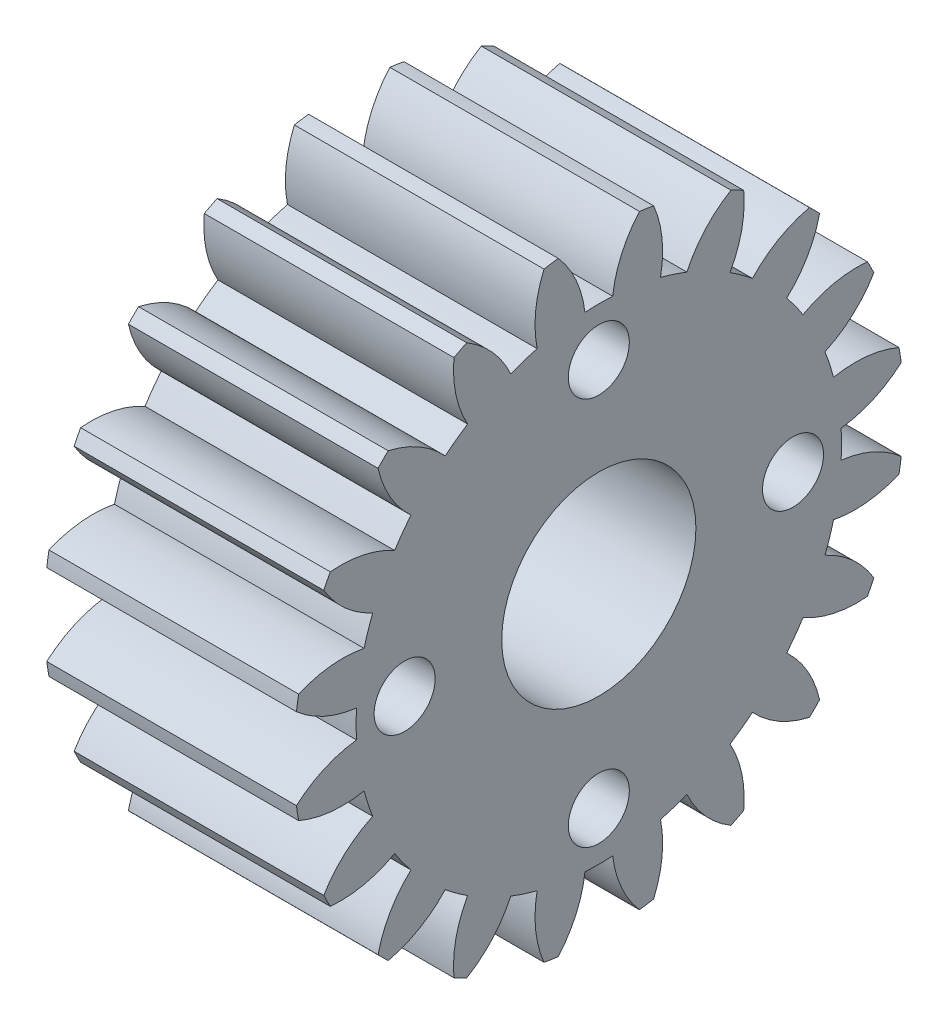
SolidWorks part; units mm, degrees
ref_plane "Plane1" through (0, 0, 0) normal (0, 0, 1) x (1, 0, 0)
ref_plane "Plane2" through (0, 0, 0) normal (0, 1, 0) x (1, 0, 0)
ref_plane "Plane3" through (0, 0, 0) normal (1, 0, 0) x (0, 0, -1)
other "Configuration Table"
sketch "HoldingSke" plane through (0, 0, 0) normal (0, 1, 0) x (1, 0, 0)
  line L0 (0, 0) -> (0.9397, -0.342)
  line L1 (-15, 0) -> (100, 0) construction
  line L2 (0, 0) -> (-2.1039, 2.3779)
  line L3 (0, 0) -> (-11.863, 4.5341)
  line L4 (0, 0) -> (8.1152, 2.9537)
  line L5 (0, 0) -> (-46.8476, -17.4728)
  line L6 (0, 0) -> (-4.1448, -2.7965)
  line L7 (-2.1039, 2.3779) -> (8.6586, 51.2059)
  line L8 (-76.2, 54.61) -> (-74.8, 54.61)
  line L9 (-71.009, 38.7566) -> (-53.1078, 45.2721)
  line L10 (-76.2, 71.12) -> (104.1128, 71.12)
  line L11 (0, 0) -> (-5, 0)
  line L12 (-76.2, 101.6) -> (-76.162, 101.6)
  line L13 (24.9733, 27.94) -> (52.9518, 28.4284)
  line L14 (24.9733, 27.94) -> (24.9743, 27.94)
  line L15 (24.9733, 27.94) -> (100.4006, 29.5858)
  line L16 (-63.627, -1) -> (-12.827, -1)
  circle A0 centre (0, 0) radius 4
  circle A1 centre (0, 0) radius 8.749
  circle A2 centre (0, 0) radius 37.5
  circle A3 centre (0, 0) radius 4
  dimension "MHD" = 17.498
  dimension "Hub_dia" = 75
  dimension "Bore" = 8
  dimension "MBD" = 8
  dimension "Num_teeth" = 20
  dimension "Pitch" = 1
  dimension "Overall_len" = 50
  dimension "Show_teeth" = 20
  dimension "Thickness" = 5
  dimension "OAL" = 50.0001
  dimension "T_dim" = 1.4
  dimension "Ap" = 20
  dimension "H" = 19.05
  dimension "Pitch_radius" = 180.3128
  dimension "Width" = 5
  dimension "Backlash" = 0.038
  dimension "Addendum_fac" = 1
  dimension "Dedendum_fac" = 1.25
  dimension "Clearance_fac" = 0.25
  dimension "Dedendum_add" = 0.001
  dimension "Module" = 1
sketch "BasProSke" plane through (0, 0, 0) normal (0, 1, 0) x (1, 0, 0)
  line L0 (-10, 0) -> (60, 0) construction
  line L1 (0, 0) -> (0, 11)
  line L2 (0, 0) -> (9, 0)
  line L3 (9, 0) -> (9, 11)
  line L4 (9, 11) -> (0, 11)
  dimension "Thickness" = 9
  dimension "Diameter" = 22
revolve "Base-Revolve" add sketch "BasProSke" angle 360 about L0
sketch "TooCutSke" plane through (0, 0, 0) normal (1, 0, 0) x (0, 0, -1)
  line L1 (0, 0) -> (0, 107) construction
  line L2 (0, 0) -> (-0.8511, 9.9637) construction
  line L3 (0, 0) -> (-3.1206, 19.7028) construction
  line L4 (-0.8511, 9.9637) -> (-1.5603, 9.8514) construction
  arc A0 (0.4999, 8.7347) -> (-0.4999, 8.7347) centre (0, 0) ccw
  arc A1 (1.4852, 10.9249) -> (-1.4852, 10.9249) centre (0, 0) ccw
  circle A2 centre (0, 0) radius 10 construction
  circle A3 centre (0, 0) radius 9.3969 construction
  arc A4 (-0.4999, 8.7347) -> (-1.4852, 10.9249) centre (-4.4722, 8.2645) ccw
  arc A5 (1.4852, 10.9249) -> (0.4999, 8.7347) centre (4.4722, 8.2645) ccw
  dimension "Root_dia" = 17.498
  dimension "Overcut_dia" = 22.0508
  dimension "Pitch_dia" = 20
  dimension "Base_dia" = 18.7939
  dimension "Flank_rad" = 4
  dimension "Half_ang" = 9
  dimension "Half_CT" = 0.7181
extrude "ToothCut" cut sketch "TooCutSke" along normal through all
fillet "Breaks" [suppressed] radius 0.02
fillet "RootFillets" [suppressed] radius 0.251
pattern_circular "TeethCuts" count 20 every 18 about axis through (-10, 0, 0) along (1, 0, 0) of "ToothCut", "RootFillets", "Breaks"
sketch "HubNeaOneSke" plane through (0, 0, 0) normal (-1, 0, 0) x (0, 0, 1)
  circle A0 centre (0, 0) radius 8.749
  dimension "Diameter" = 17.498
extrude "HubNearOne" [suppressed] add sketch "HubNeaOneSke" along normal blind 41.0001
sketch "HubNeaBotSke" plane through (0, 0, 0) normal (-1, 0, 0) x (0, 0, 1)
  circle A0 centre (0, 0) radius 8.749
  dimension "Diameter" = 17.498
extrude "HubNearBoth" [suppressed] add sketch "HubNeaBotSke" along normal blind 20.5
ref_plane "FarPln" through (9, 0, 0) normal (1, 0, 0) x (0, 0, -1)
sketch "HubFarSke" plane through (9, 0, 0) normal (1, 0, 0) x (0, 0, -1)
  circle A0 centre (0, 0) radius 8.749
  dimension "Diameter" = 17.498
extrude "HubFar" [suppressed] add sketch "HubFarSke" along normal blind 20.5
sketch "BorSke" plane through (0, 0, 0) normal (1, 0, 0) x (0, 0, -1)
  circle A0 centre (0, 0) radius 3.5
  dimension "Diameter" = 7
extrude "Bore" cut sketch "BorSke" along normal mid plane 100.0001
sketch "KeySke" plane through (0, 0, 0) normal (1, 0, 0) x (0, 0, -1)
  line L0 (-1.5, 0) -> (-1.5, 5.4)
  line L1 (-1.5, 5.4) -> (1.5, 5.4)
  line L2 (1.5, 5.4) -> (1.5, 0)
  line L3 (0, 0) -> (0, 34) construction
  line L4 (-1.5, 0) -> (1.5, 0)
  dimension "Offset" = 5.4
  dimension "Width" = 3
extrude "Keyway" [suppressed] cut sketch "KeySke" along normal mid plane 100.0001
pattern_circular "Keyway2" [suppressed] count 2 every 90 about axis through (-10, 0, 0) along (1, 0, 0)
sketch "Sketch1" plane through (9, 0, 0) normal (1, 0, 0) x (0, 0, -1)
  line L0 (-7, 0) -> (7, 0) construction
  circle A0 centre (0, -7) radius 1.1
  circle A1 centre (0, 7) radius 1.1
  circle A2 centre (7, 0) radius 1.1
  circle A3 centre (-7, 0) radius 1.1
  point P5 (0, 0)
  dimension "D1" = 2.2
  dimension "D2" = 2.2
  dimension "D3" = 14
extrude "Cut-Extrude1" cut sketch "Sketch1" against normal through all
equation "' \"Module@HoldingSke\" = 6.35"
equation "' \"Num_teeth@HoldingSke\" = 12"
equation "' \"Ap@HoldingSke\" =  20"
equation "' \"Ap@HoldingSke\" = 20"
equation "' \"Width@HoldingSke\" = 0.5 * 25.4"
equation "' \"Hub_dia@HoldingSke\"= 1 * 25.4"
equation "' \"Hub_dia@HoldingSke\" = 1 * 25.4"
equation "' \"Overall_len@HoldingSke\" = 1.0 * 25.4"
equation "' \"Bore@HoldingSke\" = 0.75 * 25.4"
equation "' \"T_dim@HoldingSke\" = 0.1 * 25.4"
equation "' \"Width@KeySke\" = 0.25 * 25.4"
equation "' \"Show_teeth@HoldingSke\" = 13"
equation "' \"Backlash@HoldingSke\" = 0.009 * 25.4"
equation "' \"Addendum_fac@HoldingSke\" = 1.0"
equation "' \"Dedendum_fac@HoldingSke\" = 1.25"
equation "' \"Dedendum_add@HoldingSke\" = 0.00005 * 25.4"
equation "' \"Clearance_fac@HoldingSke\" = 0.25"
equation "\"Pitch@HoldingSke\" = 1 / \"Module@HoldingSke\""
equation "\"Overcut_dia@TooCutSke\" = (\"Num_teeth@HoldingSke\" + 2 * \"Addendum_fac@HoldingSke\") / \"Pitch@HoldingSke\" + 0.002 * 25.4"
equation "\"Pitch_dia@TooCutSke\" = \"Num_teeth@HoldingSke\" / \"Pitch@HoldingSke\""
equation "\"Base_dia@TooCutSke\" = \"Num_teeth@HoldingSke\" / \"Pitch@HoldingSke\" * cos((\"Ap@HoldingSke\"  * 3.14159265 / 180))"
equation "\"Root_dia@TooCutSke\" = (\"Num_teeth@HoldingSke\" + 2) / \"Pitch@HoldingSke\" - 2 * (\"Addendum_fac@HoldingSke\" + \"Dedendum_fac@HoldingSke\") / \"Pitch@HoldingSke\" - \"Dedendum_add@HoldingSke\" * 2"
equation "\"Half_ang@TooCutSke\" = 180 / \"Num_teeth@HoldingSke\""
equation "\"Half_CT@TooCutSke\" = \"Num_teeth@HoldingSke\" / \"Pitch@HoldingSke\" * sin((3.14159265 / 2 / \"Num_teeth@HoldingSke\")) / 2 - 7 * \"Backlash@HoldingSke\" / 4"
equation "\"Flank_rad@TooCutSke\" = \"Num_teeth@HoldingSke\" / \"Pitch@HoldingSke\" / 5"
equation "\"Radius@RootFillets\" = \"Clearance_fac@HoldingSke\" / \"Pitch@HoldingSke\" + \"Dedendum_add@HoldingSke\""
equation "\"Break_rad@Breaks\" = 0.02 / \"Pitch@HoldingSke\""
equation "\"Thickness@HoldingSke\" = \"Width@HoldingSke\""
equation "\"OAL@HoldingSke\" = \"Thickness@HoldingSke\""
equation "\"MHD@HoldingSke\" = (\"Num_teeth@HoldingSke\" + 2) / \"Pitch@HoldingSke\" - 2 * (\"Addendum_fac@HoldingSke\" + \"Dedendum_fac@HoldingSke\")  / \"Pitch@HoldingSke\" - \"Dedendum_add@HoldingSke\" * 2"
equation "\"MBD@HoldingSke\" = (\"Num_teeth@HoldingSke\" + 2) / \"Pitch@HoldingSke\" - 2 * (\"Addendum_fac@HoldingSke\" + \"Dedendum_fac@HoldingSke\")  / \"Pitch@HoldingSke\" - \"Dedendum_add@HoldingSke\" * 2 - 0.002 * 25.4"
equation "\"MHD@HoldingSke\" = ((sgn( \"MHD@HoldingSke\" - \"Hub_dia@HoldingSke\" )-1)*( \"MHD@HoldingSke\" - \"Hub_dia@HoldingSke\" ))/-2+ \"Hub_dia@HoldingSke\""
equation "\"MBD@HoldingSke\" = ((sgn( \"MBD@HoldingSke\" - \"Bore@HoldingSke\" )-1)*( \"MBD@HoldingSke\" - \"Bore@HoldingSke\" ))/-2+ \"Bore@HoldingSke\""
equation "\"OAL@HoldingSke\" = ((sgn( \"OAL@HoldingSke\" - \"Overall_len@HoldingSke\" )+1)*( \"OAL@HoldingSke\" - \"Overall_len@HoldingSke\" ))/2 + \"Overall_len@HoldingSke\" + 0.000002 * 25.4"
equation "\"Num_teeth@TeethCuts\" = int( \"Show_teeth@HoldingSke\" ) + 1"
equation "\"Num_teeth@TeethCuts\" = ((sgn( \"Num_teeth@TeethCuts\" - \"Num_teeth@HoldingSke\" )-1)*( \"Num_teeth@TeethCuts\" - \"Num_teeth@HoldingSke\" ))/-2+ \"Num_teeth@HoldingSke\""
equation "\"Num_teeth@TeethCuts\" = ((sgn( \"Num_teeth@TeethCuts\" - 2.0)+1)*( \"Num_teeth@TeethCuts\" - 2.0))/2 +2.0"
equation "\"Angle@TeethCuts\" = 360.0 / \"Num_teeth@HoldingSke\""
equation "\"Diameter@BasProSke\" = (\"Num_teeth@HoldingSke\" + 2 * \"Addendum_fac@HoldingSke\") / \"Pitch@HoldingSke\""
equation "' \"Fillet_rad@BasProSke\" =  \"Thickness@HoldingSke\" * 0.05"
equation "' \"Fillet_rad@BasProSke\" = \"Thickness@HoldingSke\" * 0.05"
equation "\"MHD@HoldingSke\" = ((sgn( \"MHD@HoldingSke\" - \"Root_dia@TooCutSke\" )-1)*( \"MHD@HoldingSke\" - \"Root_dia@TooCutSke\" ))/-2+ \"Root_dia@TooCutSke\""
equation "\"Diameter@HubNeaOneSke\" = \"MHD@HoldingSke\""
equation "\"Length@HubNearOne\" = \"OAL@HoldingSke\" - \"Thickness@BasProSke\""
equation "\"Diameter@HubNeaBotSke\" = \"MHD@HoldingSke\""
equation "\"Length@HubNearBoth\" = ( \"OAL@HoldingSke\" - \"Thickness@BasProSke\" ) / 2.0"
equation "\"Thickness@FarPln\" = \"Thickness@BasProSke\""
equation "\"Diameter@HubFarSke\" = \"MHD@HoldingSke\""
equation "\"Length@HubFar\" = ( \"OAL@HoldingSke\" - \"Thickness@BasProSke\" ) / 2.0"
equation "\"D1@Bore\" = \"OAL@HoldingSke\" * 2.0"
equation "\"D1@Keyway\" = \"OAL@HoldingSke\" * 2.0"
equation "\"Offset@KeySke\" = \"T_dim@HoldingSke\" + \"MBD@HoldingSke\" / 2.0"
